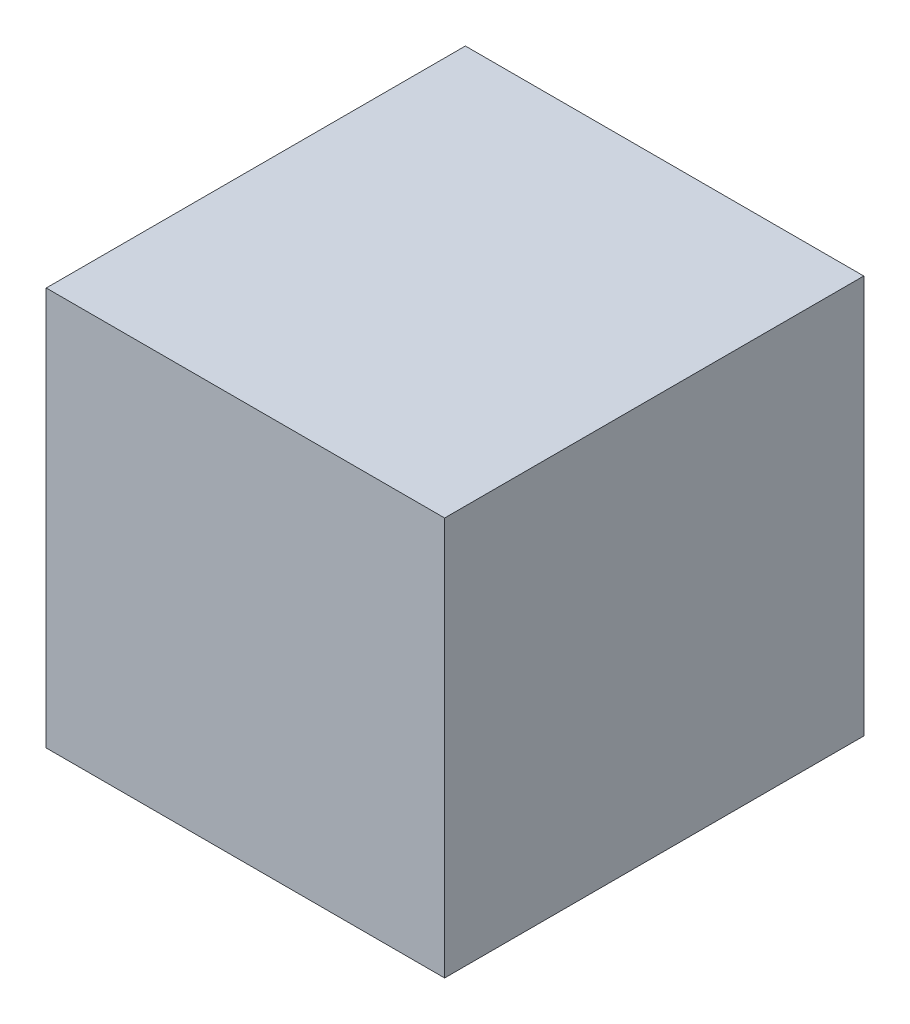
SolidWorks part; units mm, degrees
ref_plane "Alzado" through (0, 0, 0) normal (0, 0, 1) x (1, 0, 0)
ref_plane "Planta" through (0, 0, 0) normal (0, 1, 0) x (1, 0, 0)
ref_plane "Vista lateral" through (0, 0, 0) normal (1, 0, 0) x (0, 0, -1)
sketch "Croquis2" plane through (0, 0, 0) normal (0, 1, 0) x (1, 0, 0)
  line L1 (240, -252.5) -> (-240, -252.5)
  line L2 (240, -252.5) -> (240, 252.5)
  line L3 (240, 252.5) -> (-240, 252.5)
  line L4 (-240, -252.5) -> (-240, 252.5)
  line L5 (240, -252.5) -> (-240, 252.5) construction
  line L6 (240, 252.5) -> (-240, -252.5) construction
  point P0 (0, 0)
  dimension "D1" = 505
  dimension "D2" = 480
extrude "Saliente-Extruir1" add sketch "Croquis2" along normal blind 480 contours L2 L1 L4 L3
sketch "Croquis3" plane through (0, 0, -252.5) normal (0, 0, -1) x (-1, 0, 0)
  line L12 (235, 475) -> (235, 5)
  line L13 (235, 5) -> (-235, 5)
  line L14 (-235, 5) -> (-235, 475)
  line L15 (-235, 475) -> (235, 475)
extrude "Cortar-Extruir1" cut sketch "Croquis3" against normal blind 200
sketch "Croquis5" plane through (0, 0, -52.5) normal (0, 0, -1) x (-1, 0, 0)
  line L0 (-235, 5) -> (-235, 15)
  line L5 (-235, 475) -> (-235, 5) construction
  line L8 (-235, 475) -> (-235, 465)
  line L9 (-235, 475) -> (-235, 5) construction
  line L16 (225, 465) -> (225, 15)
  line L17 (225, 465) -> (-225, 465)
  line L18 (-225, 465) -> (-225, 15)
  line L19 (-225, 15) -> (225, 15)
extrude "Cortar-Extruir2" cut sketch "Croquis5" against normal blind 300 contours L17 L16 L19 L18
sketch "Croquis7" plane through (-240, 0, 0) normal (-1, 0, 0) x (0, 0, 1)
  circle A0 centre (102.5, 240) radius 125
extrude "Cortar-Extruir3" cut sketch "Croquis7" against normal blind 300
